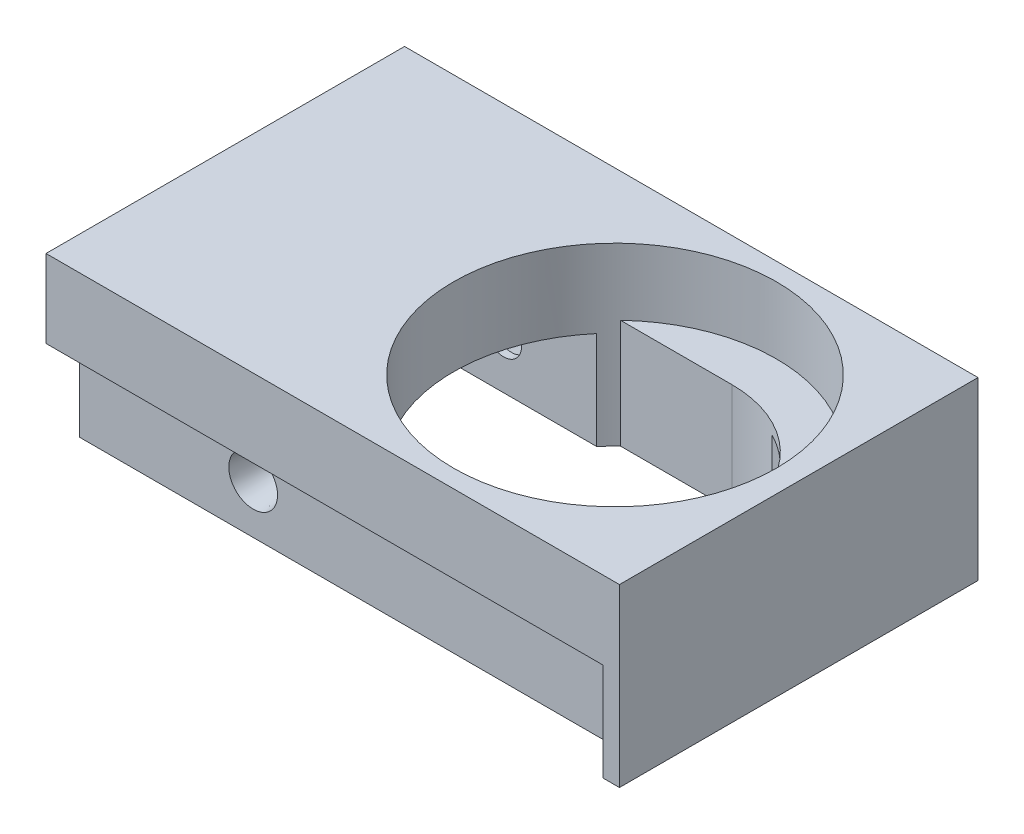
SolidWorks part; units mm, degrees
material "6061-T6 (SS)"
ref_plane "Front Plane" through (0, 0, 0) normal (0, 0, 1) x (1, 0, 0)
ref_plane "Top Plane" through (0, 0, 0) normal (0, 1, 0) x (1, 0, 0)
ref_plane "Right Plane" through (0, 0, 0) normal (1, 0, 0) x (0, 0, -1)
sketch "Sketch1" plane through (0, 0, 0) normal (0, 1, 0) x (1, 0, 0)
  line L0 (-31.75, 12.192) -> (2.5329, 12.192)
  line L1 (-31.75, -16.637) -> (31.75, -16.637)
  line L2 (-31.75, -16.637) -> (-31.75, 16.637)
  line L3 (-31.75, 16.637) -> (31.75, 16.637)
  line L4 (31.75, -16.637) -> (31.75, 16.637)
  line L5 (-31.75, -16.637) -> (31.75, 16.637) construction
  line L6 (-31.75, 16.637) -> (31.75, -16.637) construction
  line L7 (22.8671, 12.192) -> (31.75, 12.192)
  line L8 (0, 0) -> (-0.635, 0) construction
  line L9 (22.8671, -12.192) -> (31.75, -12.192)
  line L10 (-31.75, -12.192) -> (2.5329, -12.192)
  circle A0 centre (12.7, 0) radius 13.335
  arc A1 (2.5329, 12.192) -> (2.5329, -12.192) centre (12.7, 0) ccw
  arc A2 (22.8671, -12.192) -> (22.8671, 12.192) centre (12.7, 0) ccw
  point P0 (0, 0)
  dimension "D3" = 26.67
  dimension "D5" = 2.54
  dimension "D1" = 33.274
  dimension "D2" = 63.5
  dimension "D4" = 19.05
  dimension "D6" = 4.445
extrude "Boss-Extrude1" add sketch "Sketch1" along normal blind 11.1608 contours L9 A2 L7 L4 L3 L2 L0 A1 L10 L1 A0 | A1 L0 L2 L10 | A2 L9 L4 L7
sketch "Sketch2" plane through (0, 11.1608, 0) normal (0, 1, 0) x (1, 0, 0)
  line L0 (31.75, -16.637) -> (31.75, 16.637) construction
  line L1 (-31.75, -20.447) -> (31.75, -20.447)
  line L2 (-31.75, -20.447) -> (-31.75, 20.447)
  line L3 (-31.75, 20.447) -> (31.75, 20.447)
  line L4 (31.75, -20.447) -> (31.75, 20.447)
  line L5 (-31.75, -20.447) -> (31.75, 20.447) construction
  line L6 (-31.75, 20.447) -> (31.75, -20.447) construction
  line L7 (-31.75, 16.637) -> (31.75, 16.637) construction
  circle A0 centre (12.7, 0) radius 18.415
  point P0 (0, 0)
  dimension "D2" = 36.83
  dimension "D1" = 3.81
sketch "Sketch3" plane through (0, 11.1608, 0) normal (0, 1, 0) x (1, 0, 0)
  line L0 (-31.75, -16.637) -> (31.75, -16.637) construction
  line L1 (-31.75, -20.447) -> (31.75, -20.447)
  line L2 (-31.75, -20.447) -> (-31.75, 20.447)
  line L3 (-31.75, 20.447) -> (31.75, 20.447)
  line L4 (31.75, -20.447) -> (31.75, 20.447)
  line L5 (-31.75, -20.447) -> (31.75, 20.447) construction
  line L6 (-31.75, 20.447) -> (31.75, -20.447) construction
  circle A0 centre (12.7, 0) radius 13.335
  circle A1 centre (12.7, 0) radius 13.335 construction
  point P0 (0, 0)
  dimension "D1" = 3.81
extrude "Boss-Extrude4" add sketch "Sketch3" along normal blind 1.27
extrude "Boss-Extrude5" add sketch "Sketch2" along normal blind 3.81 from surface at 1.27 starting at face at (0, 12.4308, 0)
sketch "Sketch4" plane through (0, 0, 0) normal (0, -1, 0) x (1, 0, 0)
  line L0 (31.75, 16.637) -> (31.75, -16.637) construction
  line L1 (-31.75, 11.938) -> (31.75, 11.938)
  line L2 (-31.75, 11.938) -> (-31.75, -11.938)
  line L3 (-31.75, -11.938) -> (31.75, -11.938)
  line L4 (31.75, 11.938) -> (31.75, -11.938)
  line L5 (-31.75, 11.938) -> (31.75, -11.938) construction
  line L6 (-31.75, -11.938) -> (31.75, 11.938) construction
  line L7 (-31.75, -16.637) -> (31.75, -16.637) construction
  point P0 (0, 0)
  dimension "D1" = 4.699
extrude "Cut-Extrude1" cut sketch "Sketch4" against normal up to surface (11.1608 mm away) up to face at (0, 11.1608, 18.542)
sketch "Sketch5" plane through (0, 0, -16.637) normal (0, 0, -1) x (-1, 0, 0)
  line L0 (-31.75, 11.1608) -> (-31.75, 0) construction
  line L1 (31.75, 5.5804) -> (11.9304, 5.5804) construction
  line L2 (31.75, 11.1608) -> (31.75, 0) construction
  circle A0 centre (11.9304, 5.5804) radius 2.7813
  dimension "D1" = 43.6804
  dimension "D2" = 5.5626
extrude "Cut-Extrude2" cut sketch "Sketch5" against normal blind 3.81 draft 8
sketch "Sketch6" plane through (0, 0, -12.827) normal (0, 0, -1) x (-1, 0, 0)
  circle A0 centre (11.9304, 5.5804) radius 2.032
  dimension "D1" = 4.064
extrude "Cut-Extrude3" cut sketch "Sketch6" against normal through all
mirror "Mirror1" about plane through (0, 0, 0) normal (0, 0, 1) of "Cut-Extrude2"
sketch "Sketch7" plane through (0, 12.4308, 0) normal (0, 1, 0) x (1, 0, 0)
  line L0 (12.7, 13.335) -> (0, 13.335)
  line L1 (12.7, -13.335) -> (0, -13.335)
  circle A0 centre (12.7, 0) radius 13.335 construction
  circle A1 centre (12.7, 0) radius 18.415 construction
  arc A2 (0, 13.335) -> (0, -13.335) centre (12.7, 0) ccw
  arc A3 (12.7, 13.335) -> (12.7, -13.335) centre (12.7, 0) ccw
extrude "Cut-Extrude4" cut sketch "Sketch7" against normal through all
sketch "Sketch8" plane through (31.75, 0, 0) normal (1, 0, 0) x (0, 0, -1)
  line L0 (-16.637, 0) -> (-11.938, 0) construction
  line L1 (20.447, 16.2408) -> (-20.447, 16.2408)
  line L2 (20.447, 16.2408) -> (20.447, 0)
  line L3 (20.447, 0) -> (-20.447, 0)
  line L4 (-20.447, 16.2408) -> (-20.447, 0)
  line L5 (-20.447, 16.2408) -> (-20.447, 11.1608) construction
extrude "Boss-Extrude6" add sketch "Sketch8" along normal blind 1.905
sketch "Sketch9" plane through (0, 16.2408, 0) normal (0, 1, 0) x (1, 0, 0)
  line L8 (-31.75, -20.447) -> (33.655, -20.447)
  line L9 (33.655, -20.447) -> (33.655, 20.447)
  line L10 (33.655, 20.447) -> (-31.75, 20.447)
  line L11 (-31.75, 20.447) -> (-31.75, -20.447)
  line L12 (-31.75, -20.447) -> (33.655, -20.447)
  line L13 (33.655, -20.447) -> (33.655, 20.447)
  line L14 (33.655, 20.447) -> (-31.75, 20.447)
  line L15 (-31.75, 20.447) -> (-31.75, -20.447)
  circle M5 centre (12.7, 0) radius 18.415
  line M6 (-31.75, -20.447) -> (33.655, -20.447)
  line M7 (33.655, -20.447) -> (33.655, 20.447)
  line M8 (33.655, 20.447) -> (-31.75, 20.447)
  line M9 (-31.75, 20.447) -> (-31.75, -20.447)
  dimension "D1" = 0
extrude "Boss-Extrude8" add sketch "Sketch9" along normal blind 3.81 contours M9 M6 M7 M8 M5
